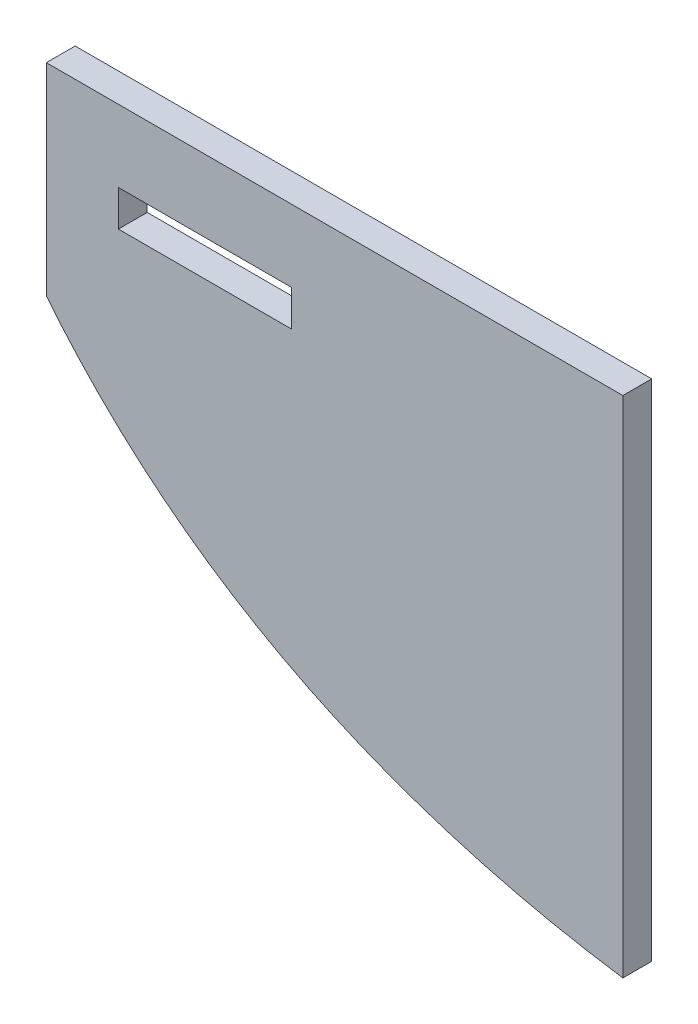
SolidWorks part; units mm, degrees
ref_plane "Plan de face" through (0, 0, 0) normal (0, 0, 1) x (1, 0, 0)
ref_plane "Plan de dessus" through (0, 0, 0) normal (0, 1, 0) x (1, 0, 0)
ref_plane "Plan de droite" through (0, 0, 0) normal (1, 0, 0) x (0, 0, -1)
sketch "Esquisse1" plane through (0, 0, 0) normal (0, 0, 1) x (1, 0, 0)
  line L1 (-20, -17.5) -> (20, -17.5)
  line L2 (-20, -17.5) -> (-20, 17.5)
  line L3 (-20, 17.5) -> (20, 17.5)
  line L4 (20, -17.5) -> (20, 17.5)
  line L5 (-20, -17.5) -> (20, 17.5) construction
  line L6 (-20, 17.5) -> (20, -17.5) construction
  line L7 (-15, 10) -> (-3, 10)
  line L8 (-15, 10) -> (-15, 12.5)
  line L9 (-15, 12.5) -> (-3, 12.5)
  line L10 (-3, 10) -> (-3, 12.5)
  point P0 (0, 0)
  dimension "D1" = 40
  dimension "D2" = 35
  dimension "D3" = 2.5
  dimension "D4" = 12
  dimension "D5" = 5
  dimension "D6" = 5
extrude "Boss.-Extru.1" add sketch "Esquisse1" along normal blind 2
sketch "Esquisse2" plane through (0, 0, 2) normal (0, 0, 1) x (1, 0, 0)
  line L0 (-20, 17.5) -> (-20, -17.5) construction
  line L1 (-28.0307, 16.9365) -> (-23.254, -35.4795)
  line L2 (-23.254, -35.4795) -> (20, -17.5)
  spline S0 degree 2 poles (20, -17.5) (-15.3607, -12.2695) (-28.0307, 16.9365) knots 0 0 0 1 1 1
extrude "Enlèv. mat.-Extru.1" cut sketch "Esquisse2" against normal blind 10
